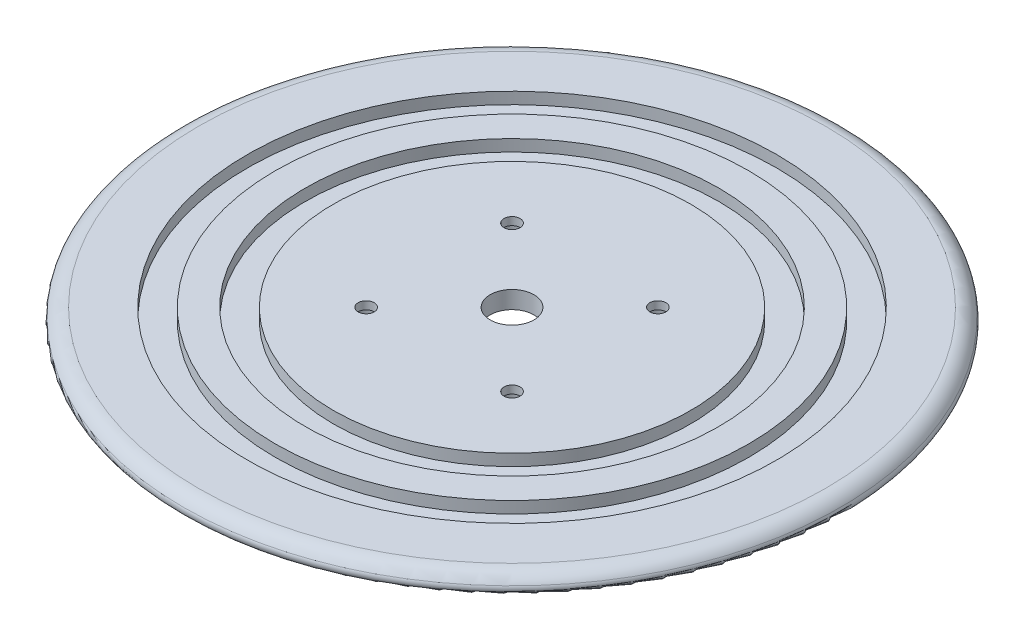
SolidWorks part; units mm, degrees
ref_plane "Front Plane" through (0, 0, 0) normal (0, 0, 1) x (1, 0, 0)
ref_plane "Top Plane" through (0, 0, 0) normal (0, 1, 0) x (1, 0, 0)
ref_plane "Right Plane" through (0, 0, 0) normal (1, 0, 0) x (0, 0, -1)
sketch "Sketch2" plane through (0, 0, 0) normal (0, 0, 1) x (1, 0, 0)
  line L3 (0, 0) -> (-61.26, 0)
  line L4 (-61.26, 0) -> (-61.26, -4)
  line L5 (-61.26, -4) -> (-70.86, -4)
  line L6 (-70.86, -4) -> (-70.86, 0)
  line L7 (-70.86, 0) -> (-81.13, 0)
  line L8 (-81.13, 0) -> (-81.13, -4)
  line L9 (-81.13, -4) -> (-90.73, -4)
  line L10 (-90.73, -4) -> (-90.73, 0)
  line L11 (-90.73, 0) -> (-107.5, 0)
  line L12 (-113.5, -6) -> (0, -6)
  line L13 (0, -6) -> (0, 0)
  arc A1 (-107.5, 0) -> (-113.5, -6) centre (-107.5, -6) ccw
  dimension "D2" = 9.6
  dimension "D8" = 6
  dimension "D1" = 113.5
  dimension "D3" = 9.6
  dimension "D4" = 10.27
  dimension "D5" = 4
  dimension "D6" = 4
  dimension "D7" = 61.26
revolve "Revolve1" add sketch "Sketch2" angle 360 about L13
sketch "Sketch3" plane through (0, -6, 0) normal (0, -1, 0) x (1, 0, 0)
  line L1 (-25, 25) -> (25, 25)
  line L2 (-25, 25) -> (-25, -25)
  line L3 (-25, -25) -> (25, -25)
  line L4 (25, 25) -> (25, -25)
  line L5 (-25, 25) -> (25, -25) construction
  line L6 (-25, -25) -> (25, 25) construction
  point P0 (0, 0)
  dimension "D1" = 50
  dimension "D2" = 50
hole_wizard "CBORE for M5 Cheese Head Screw1" positions "Sketch4" profile "Sketch5" counterbore size "M5" standard "AS" end condition through all
sketch "Sketch4" plane through (0, -6, 0) normal (0, -1, 0) x (-1, 0, 0)
  point P0 (25, -25)
  point P3 (-25, -25)
  point P6 (-25, 25)
  point P9 (25, 25)
sketch "Sketch5" plane through (-25, -6, 25) normal (1, 0, 0) x (0, 0, -1)
  line L0 (0, 0) -> (0, 6)
  line L1 (0, 6) -> (2.75, 6)
  line L3 (2.75, 6) -> (2.75, 3.3)
  line L4 (2.75, 3.3) -> (4.75, 3.3)
  line L5 (4.75, 3.3) -> (4.75, 0)
  line L7 (4.75, 0) -> (0, 0)
  line L11 (0, -6.35) -> (0, 107.95) construction
  dimension "Thru Hole Dia." = 5.5
  dimension "Thru Hole Depth" = 6
  dimension "C'Bore Dia." = 9.5
  dimension "C'Bore Depth" = 3.3
fillet "Fillet1" radius 2 1 edges at (0, -6, -113.5)
sketch "Sketch6" plane through (0, -6, 0) normal (0, -1, 0) x (1, 0, 0)
  circle A0 centre (0, 0) radius 7.5
  dimension "D1" = 15
extrude "Cut-Extrude1" cut sketch "Sketch6" against normal through all
